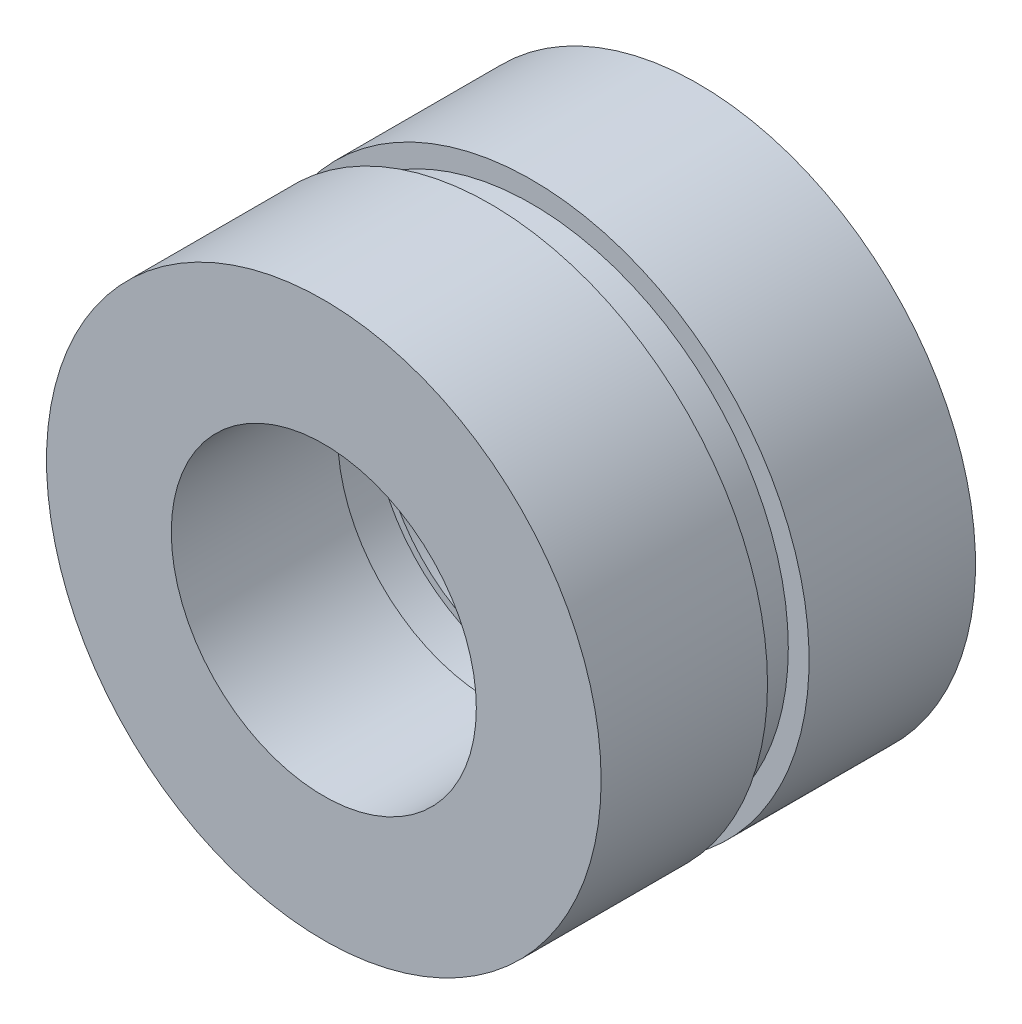
SolidWorks part; units mm, degrees
ref_plane "Front Plane" through (0, 0, 0) normal (0, 0, 1) x (1, 0, 0)
ref_plane "Top Plane" through (0, 0, 0) normal (0, 1, 0) x (1, 0, 0)
ref_plane "Right Plane" through (0, 0, 0) normal (1, 0, 0) x (0, 0, -1)
sketch "Sketch1" plane through (0, 0, 0) normal (0, 0, 1) x (1, 0, 0)
  circle A0 centre (0, 0) radius 2.921
  circle A1 centre (0, 0) radius 4.699
  dimension "D1" = 1.778
  dimension "D2" = 5.842
extrude "Boss-Extrude2" add sketch "Sketch1" along normal blind 0.762 contours A1
sketch "Sketch3" plane through (0, 0, 0.762) normal (0, 0, 1) x (1, 0, 0)
  circle A0 centre (0, 0) radius 2.794
  circle A1 centre (0, 0) radius 5.08
  dimension "D1" = 2.286
  dimension "D2" = 5.588
extrude "Boss-Extrude3" add sketch "Sketch3" along normal blind 3.048
sketch "Sketch4" plane through (0, 0, 0) normal (0, 0, -1) x (-1, 0, 0)
  circle A0 centre (0, 0) radius 2.794
  circle A1 centre (0, 0) radius 5.08
  dimension "D1" = 5.588
  dimension "D2" = 10.16
extrude "Boss-Extrude4" add sketch "Sketch4" along normal blind 3.048 separate body
